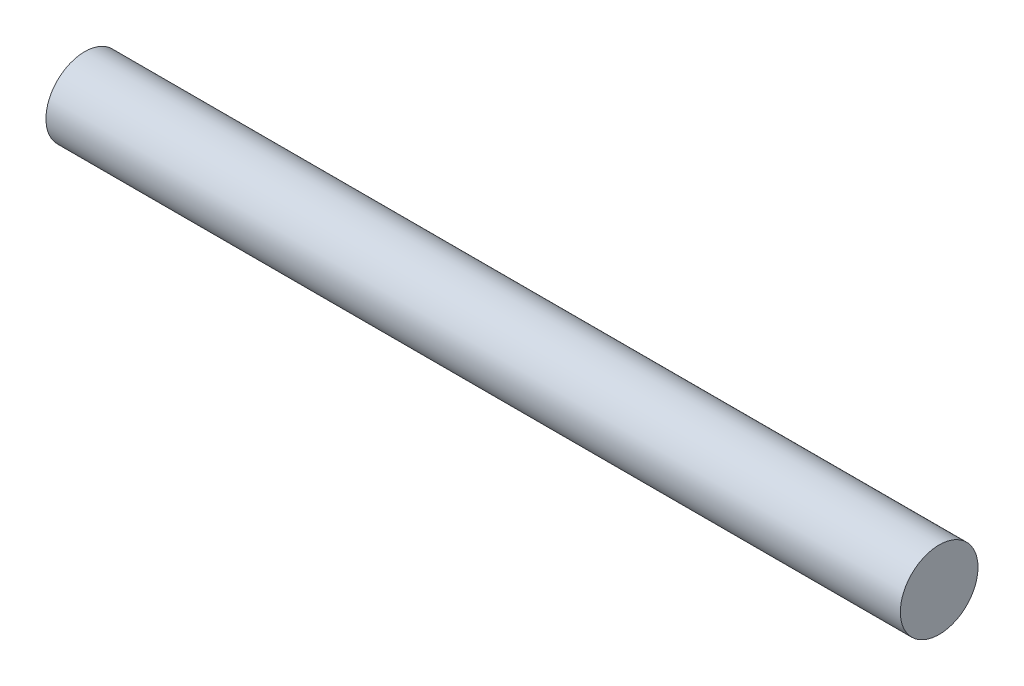
SolidWorks part; units mm, degrees
ref_plane "Płaszczyzna przednia" through (0, 0, 0) normal (0, 0, 1) x (1, 0, 0)
ref_plane "Płaszczyzna górna" through (0, 0, 0) normal (0, 1, 0) x (1, 0, 0)
ref_plane "Płaszczyzna prawa" through (0, 0, 0) normal (1, 0, 0) x (0, 0, -1)
sketch "Szkic1" plane through (0, 0, 0) normal (1, 0, 0) x (0, 0, -1)
  circle A1 centre (0, 0) radius 2.5
extrude "Dodanie-wyciągnięcie1" add sketch "Szkic1" along normal mid plane 55
